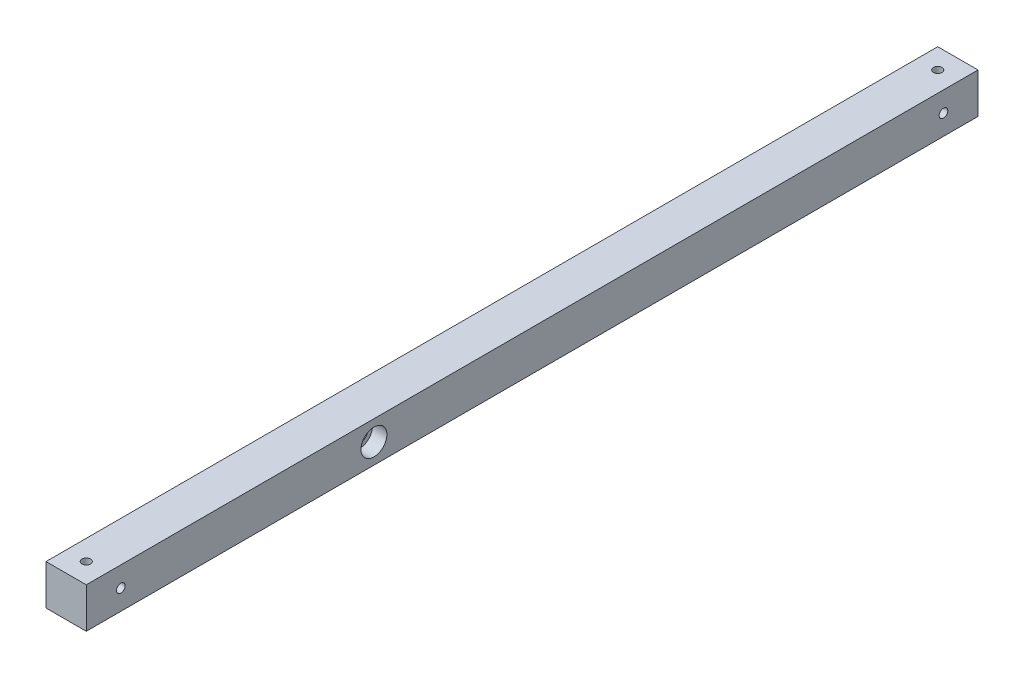
SolidWorks part; units mm, degrees
ref_plane "Ön Düzlem" through (0, 0, 0) normal (0, 0, 1) x (1, 0, 0)
ref_plane "Üst Düzlem" through (0, 0, 0) normal (0, 1, 0) x (1, 0, 0)
ref_plane "Sağ Düzlem" through (0, 0, 0) normal (1, 0, 0) x (0, 0, -1)
sketch "Çizim1" plane through (0, 0, 0) normal (0, 0, 1) x (1, 0, 0)
  line L1 (-14, -14) -> (14, -14)
  line L2 (-14, -14) -> (-14, 14)
  line L3 (-14, 14) -> (14, 14)
  line L4 (14, -14) -> (14, 14)
  line L5 (-14, -14) -> (14, 14) construction
  line L6 (-14, 14) -> (14, -14) construction
  point P0 (0, 0)
  dimension "D1" = 28
  dimension "D2" = 28
extrude "Yükseklik-Ekstrüzyon1" add sketch "Çizim1" along normal blind 620
sketch "Çizim3" plane through (0, -14, 0) normal (0, -1, 0) x (1, 0, 0)
  line L0 (-14, 524.2458) -> (14, 524.2458) construction
  line L1 (-14, 620) -> (-14, 0) construction
  line L2 (14, 620) -> (14, 0) construction
  line L3 (-14, 0) -> (14, 0) construction
  line L4 (14, 620) -> (-14, 620) construction
  circle A0 centre (0, 14) radius 3
  circle A1 centre (0, 606) radius 3
  point P11 (0, 524.2458)
  dimension "D1" = 14
  dimension "D3" = 6
  dimension "D2" = 14
extrude "Kes-Ekstrüzyon2" cut sketch "Çizim3" against normal through all
sketch "Çizim4" plane through (0, -14, 0) normal (0, -1, 0) x (1, 0, 0)
  circle A0 centre (0, 14) radius 5
  circle A1 centre (0, 606) radius 5
  dimension "D1" = 10
extrude "Kes-Ekstrüzyon3" cut sketch "Çizim4" against normal blind 7
sketch "Çizim5" plane through (14, 0, 0) normal (1, 0, 0) x (0, 0, -1)
  line L0 (-620, -14) -> (-620, 14) construction
  circle A0 centre (-420, 0) radius 6
  dimension "D2" = 12
  dimension "D1" = 200
extrude "Kes-Ekstrüzyon4" cut sketch "Çizim5" against normal through all
sketch "Çizim6" plane through (14, 0, 0) normal (1, 0, 0) x (0, 0, -1)
  circle A0 centre (-420, 0) radius 9
  dimension "D1" = 18
extrude "Kes-Ekstrüzyon5" cut sketch "Çizim6" against normal blind 10
sketch "Çizim7" plane through (-14, 0, 0) normal (-1, 0, 0) x (0, 0, 1)
  line L0 (0, 14) -> (0, -14) construction
  line L2 (620, 14) -> (620, -14) construction
  circle A0 centre (24, 0) radius 3
  circle A1 centre (596, 0) radius 3
  point P8 (0, 0)
  dimension "D1" = 6
  dimension "D3" = 24
  dimension "D2" = 24
extrude "Kes-Ekstrüzyon6" cut sketch "Çizim7" against normal through all
sketch "Çizim8" plane through (-14, 0, 0) normal (-1, 0, 0) x (0, 0, 1)
  circle A0 centre (24, 0) radius 5
  circle A1 centre (596, 0) radius 5
  dimension "D1" = 10
extrude "Kes-Ekstrüzyon7" cut sketch "Çizim8" against normal blind 7
